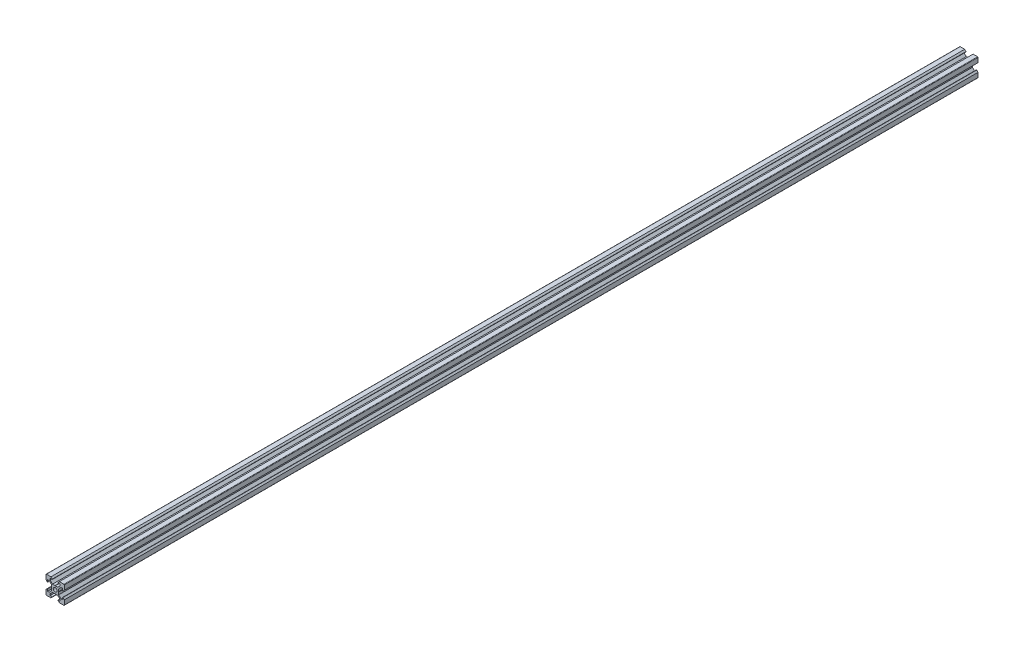
SolidWorks part; units mm, degrees
material "6061-T6 (SS)"
ref_plane "Front Plane" through (0, 0, 0) normal (0, 0, 1) x (1, 0, 0)
ref_plane "Top Plane" through (0, 0, 0) normal (0, 1, 0) x (1, 0, 0)
ref_plane "Right Plane" through (0, 0, 0) normal (1, 0, 0) x (0, 0, -1)
sketch "Sketch1" plane through (0, 0, 0) normal (0, 0, 1) x (1, 0, 0)
  line L1 (9.5, -10) -> (-9.5, -10)
  line L2 (10, -9.5) -> (10, 9.5)
  line L3 (9.5, 10) -> (-9.5, 10)
  line L4 (-10, -9.5) -> (-10, 9.5)
  line L5 (10, -10) -> (-10, 10) construction
  line L6 (10, 10) -> (-10, -10) construction
  circle A0 centre (0, 0) radius 2.1
  arc A1 (-9.5, 10) -> (-10, 9.5) centre (-9.5, 9.5) ccw
  arc A2 (10, 9.5) -> (9.5, 10) centre (9.5, 9.5) ccw
  arc A3 (9.5, -10) -> (10, -9.5) centre (9.5, -9.5) ccw
  arc A4 (-9.5, -10) -> (-10, -9.5) centre (-9.5, -9.5) cw
  point P0 (0, 0)
  line B0 (0, 0) -> (0, 10) construction
  line B1 (0, 3.69) -> (-0.21, 3.9)
  line B2 (-0.21, 3.9) -> (-2.8393, 3.9)
  line B3 (-2.8393, 3.9) -> (-5.5, 6.5607)
  line B4 (-5.5, 6.5607) -> (-5.5, 8.2)
  line B5 (-5.5, 8.2) -> (-3.125, 8.2)
  line B6 (-3.125, 8.2) -> (-3.125, 8.545)
  line B7 (-3.125, 8.545) -> (-4.58, 10)
  line B8 (-4.58, 10) -> (4.58, 10)
  line B9 (0, 0) -> (-5.9132, 5.9132) construction
  line B10 (3.125, 8.545) -> (4.58, 10)
  line B11 (3.125, 8.2) -> (3.125, 8.545)
  line B12 (5.5, 8.2) -> (3.125, 8.2)
  line B13 (5.5, 6.5607) -> (5.5, 8.2)
  line B14 (2.8393, 3.9) -> (5.5, 6.5607)
  line B15 (0.21, 3.9) -> (2.8393, 3.9)
  line B16 (0, 3.69) -> (0.21, 3.9)
  line B17 (0, 0) -> (-10, 0) construction
  line B18 (-3.69, 0) -> (-3.9, -0.21)
  line B19 (-3.9, -0.21) -> (-3.9, -2.8393)
  line B20 (-3.9, -2.8393) -> (-6.5607, -5.5)
  line B21 (-6.5607, -5.5) -> (-8.2, -5.5)
  line B22 (-8.2, -5.5) -> (-8.2, -3.125)
  line B23 (-8.2, -3.125) -> (-8.545, -3.125)
  line B24 (-8.545, -3.125) -> (-10, -4.58)
  line B25 (-10, -4.58) -> (-10, 4.58)
  line B26 (0, 0) -> (-5.9132, -5.9132) construction
  line B27 (-8.545, 3.125) -> (-10, 4.58)
  line B28 (-8.2, 3.125) -> (-8.545, 3.125)
  line B29 (-8.2, 5.5) -> (-8.2, 3.125)
  line B30 (-6.5607, 5.5) -> (-8.2, 5.5)
  line B31 (-3.9, 2.8393) -> (-6.5607, 5.5)
  line B32 (-3.9, 0.21) -> (-3.9, 2.8393)
  line B33 (-3.69, 0) -> (-3.9, 0.21)
  line B34 (0, 0) -> (0, -10) construction
  line B35 (0, -3.69) -> (0.21, -3.9)
  line B36 (0.21, -3.9) -> (2.8393, -3.9)
  line B37 (2.8393, -3.9) -> (5.5, -6.5607)
  line B38 (5.5, -6.5607) -> (5.5, -8.2)
  line B39 (5.5, -8.2) -> (3.125, -8.2)
  line B40 (3.125, -8.2) -> (3.125, -8.545)
  line B41 (3.125, -8.545) -> (4.58, -10)
  line B42 (4.58, -10) -> (-4.58, -10)
  line B43 (0, 0) -> (5.9132, -5.9132) construction
  line B44 (-3.125, -8.545) -> (-4.58, -10)
  line B45 (-3.125, -8.2) -> (-3.125, -8.545)
  line B46 (-5.5, -8.2) -> (-3.125, -8.2)
  line B47 (-5.5, -6.5607) -> (-5.5, -8.2)
  line B48 (-2.8393, -3.9) -> (-5.5, -6.5607)
  line B49 (-0.21, -3.9) -> (-2.8393, -3.9)
  line B50 (0, -3.69) -> (-0.21, -3.9)
  line B51 (0, 0) -> (10, 0) construction
  line B52 (3.69, 0) -> (3.9, 0.21)
  line B53 (3.9, 0.21) -> (3.9, 2.8393)
  line B54 (3.9, 2.8393) -> (6.5607, 5.5)
  line B55 (6.5607, 5.5) -> (8.2, 5.5)
  line B56 (8.2, 5.5) -> (8.2, 3.125)
  line B57 (8.2, 3.125) -> (8.545, 3.125)
  line B58 (8.545, 3.125) -> (10, 4.58)
  line B59 (10, 4.58) -> (10, -4.58)
  line B60 (0, 0) -> (5.9132, 5.9132) construction
  line B61 (8.545, -3.125) -> (10, -4.58)
  line B62 (8.2, -3.125) -> (8.545, -3.125)
  line B63 (8.2, -5.5) -> (8.2, -3.125)
  line B64 (6.5607, -5.5) -> (8.2, -5.5)
  line B65 (3.9, -2.8393) -> (6.5607, -5.5)
  line B66 (3.9, -0.21) -> (3.9, -2.8393)
  line B67 (3.69, 0) -> (3.9, -0.21)
sketch_block_instance "V Slot 1-4"
sketch_block "V Slot 1" parameters "D1"=10, "D2"=11, "D3"=4.3, "D4"=1.8, "D5"=0.21, "D6"=45, "D7"=9.16, "D8"=1.5, "D9"=6.25
sketch_block_instance "V Slot 1-5"
sketch_block_instance "V Slot 1-6"
sketch_block_instance "V Slot 1-7" parameters "D1"=31.2546, "D3"=0.5, "D2"=9.6469
extrude "Boss-Extrude1" add sketch "Sketch1" along normal blind 1000 contours B67 B52 B53 B54 B55 B56 B57 B58 L2 A2 L3 B10 B11 B12 B13 B14 B15 B16 B1 B2 B3 B4 B5 B6 B7 A1 L4 B27 B28 B29 B30 B31 B32 B33 B18 B19 B20 B21 B22 B23 B24 A4 L1 B44 B45 B46 B47 B48 B49
